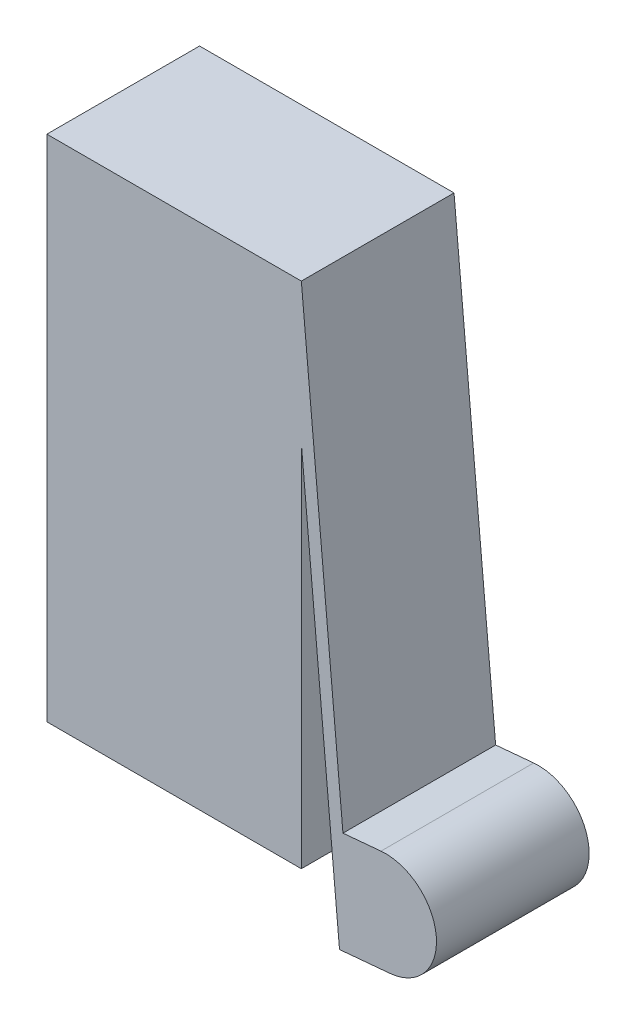
SolidWorks part; units mm, degrees
ref_plane "Płaszczyzna przednia" through (0, 0, 0) normal (0, 0, 1) x (1, 0, 0)
ref_plane "Płaszczyzna górna" through (0, 0, 0) normal (0, 1, 0) x (1, 0, 0)
ref_plane "Płaszczyzna prawa" through (0, 0, 0) normal (1, 0, 0) x (0, 0, -1)
sketch "Szkic1" plane through (0, 0, 0) normal (0, 0, 1) x (1, 0, 0)
  line L0 (10, 14.483) -> (11.5, -2)
  line L1 (0, 20) -> (10, 20)
  line L2 (0, 20) -> (0, 0)
  line L3 (0, 0) -> (10, 0)
  line L4 (10, 20) -> (10, 0)
  line L5 (10, 20) -> (11.6354, 2.0289)
  line L6 (11.5, -2) -> (13.4918, -1.8187)
  line L7 (11.6354, 2.0289) -> (13.1293, 2.1648)
  arc A0 (13.1293, 2.1648) -> (13.4918, -1.8187) centre (13.3105, 0.173) cw
  dimension "D4" = 2
  dimension "D1" = 10
  dimension "D2" = 20
  dimension "D3" = 0.5
  dimension "D5" = 2
  dimension "D6" = 1.5
  dimension "D7" = 2
extrude "Dodanie-wyciągnięcie1" add sketch "Szkic1" along normal blind 6 contours L4 L1 L2 L3 | A0 L7 L5 L4 L0 L6
